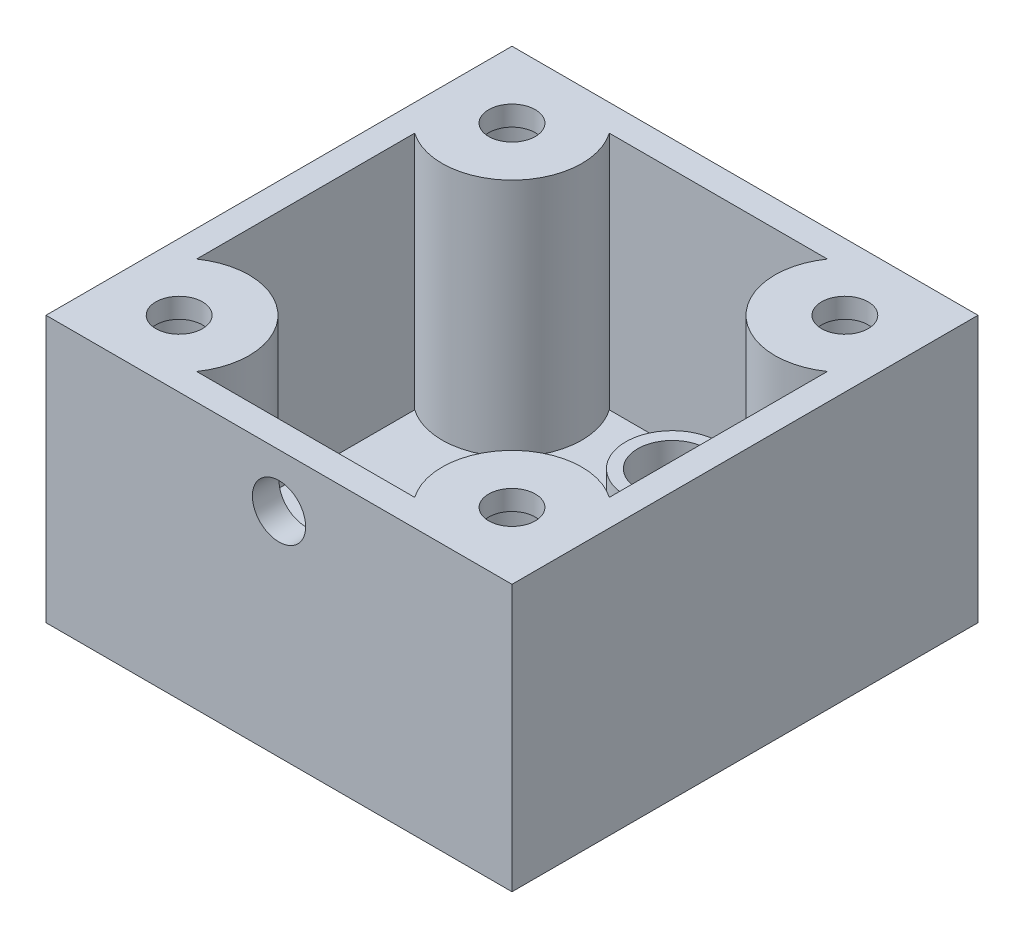
SolidWorks part; units mm, degrees
ref_plane "Front Plane" through (0, 0, 0) normal (0, 0, 1) x (1, 0, 0)
ref_plane "Top Plane" through (0, 0, 0) normal (0, 1, 0) x (1, 0, 0)
ref_plane "Right Plane" through (0, 0, 0) normal (1, 0, 0) x (0, 0, -1)
sketch "Sketch2" plane through (0, 0, 0) normal (0, 1, 0) x (1, 0, 0)
  line L1 (-17.5, -17.5) -> (17.5, -17.5)
  line L2 (-17.5, -17.5) -> (-17.5, 17.5)
  line L3 (-17.5, 17.5) -> (17.5, 17.5)
  line L4 (17.5, -17.5) -> (17.5, 17.5)
  line L5 (-17.5, -17.5) -> (17.5, 17.5) construction
  line L6 (-17.5, 17.5) -> (17.5, -17.5) construction
  point P0 (0, 0)
  dimension "D1" = 35
  dimension "D2" = 35
extrude "Boss-Extrude1" add sketch "Sketch2" against normal blind 20
sketch "Sketch3" plane through (0, 0, 0) normal (0, 1, 0) x (1, 0, 0)
  circle A0 centre (0, -4.7868) radius 6
  circle A1 centre (0, 8.5) radius 2.6
  dimension "D1" = 12
  dimension "D2" = 5.2
sketch "Sketch4" plane through (0, 0, 0) normal (0, 1, 0) x (1, 0, 0)
  line L0 (17.5, 17.5) -> (-17.5, 17.5) construction
  line L1 (-17.5, 17.5) -> (-17.5, -17.5) construction
  line L2 (-17.5, -17.5) -> (17.5, -17.5) construction
  line L3 (17.5, -17.5) -> (17.5, 17.5) construction
  circle A0 centre (-12.5, 12.5) radius 3.25
  circle A1 centre (12.5, 12.5) radius 3.25
  circle A2 centre (-12.5, -12.5) radius 3.25
  circle A3 centre (12.5, -12.5) radius 3.25
  dimension "D1" = 6.5
  dimension "D4" = 6.5
  dimension "D5" = 6.5
  dimension "D7" = 6.5
  dimension "D2" = 5
  dimension "D3" = 5
  dimension "D6" = 5
  dimension "D8" = 5
extrude "Cut-Extrude1" cut sketch "Sketch4" against normal through all from offset 1.5 offset against normal yes
extrude "holes" [suppressed] cut sketch "Sketch3" against normal through all
sketch "Sketch5" plane through (0, 0, 0) normal (0, 1, 0) x (1, 0, 0)
  line L0 (-17.5, 17.5) -> (17.5, -17.5) construction
  line L1 (-17.5, -17.5) -> (17.5, 17.5) construction
  line L2 (-8.1916, 15.5) -> (0, 15.5)
  line L3 (-15.5, 8.1916) -> (-15.5, 0)
  line L6 (17.5, 17.5) -> (-17.5, -17.5) construction
  line L7 (-17.5, 17.5) -> (17.5, -17.5) construction
  line L10 (17.5, -17.5) -> (-17.5, 17.5) construction
  line L11 (17.5, 17.5) -> (-17.5, -17.5) construction
  line L14 (-17.5, -17.5) -> (17.5, 17.5) construction
  line L15 (17.5, -17.5) -> (-17.5, 17.5) construction
  line L16 (-17.5, 17.5) -> (-17.5, -17.5) construction
  line L17 (17.5, 17.5) -> (-17.5, 17.5) construction
  line L18 (8.1916, 15.5) -> (0, 15.5)
  line L19 (15.5, 8.1916) -> (15.5, 0)
  line L20 (15.5, -8.1916) -> (15.5, 0)
  line L21 (8.1916, -15.5) -> (0, -15.5)
  line L22 (-8.1916, -15.5) -> (0, -15.5)
  line L23 (-15.5, -8.1916) -> (-15.5, 0)
  arc A0 (-8.1916, 15.5) -> (-15.5, 8.1916) centre (-12.5, 12.5) cw
  arc A1 (15.5, 8.1916) -> (8.1916, 15.5) centre (12.5, 12.5) cw
  arc A2 (8.1916, -15.5) -> (15.5, -8.1916) centre (12.5, -12.5) cw
  arc A3 (-15.5, -8.1916) -> (-8.1916, -15.5) centre (-12.5, -12.5) cw
  point P11 (-12.5, 12.5)
  point P25 (12.5, 12.5)
  point P35 (12.5, -12.5)
  point P45 (-12.5, -12.5)
  point P48 (0.3754, 0)
  point P57 (0, 0)
  dimension "D3" = 5.25
  dimension "D1" = 2
  dimension "D2" = 2
extrude "cavity" cut sketch "Sketch5" against normal offset from surface (18 mm away) 2 up to face at (-12.5, -20, 15.75)
sketch "Sketch7" plane through (0, -18, 0) normal (0, 1, 0) x (1, 0, 0)
  circle A0 centre (0, 8.5) radius 3.5
  circle A1 centre (0, 8.5) radius 2.575
  dimension "D1" = 7
extrude "LED boss" [suppressed] add sketch "Sketch7" along normal blind 2
sketch "Sketch10" plane through (0, -18, 0) normal (0, 1, 0) x (1, 0, 0)
  circle A0 centre (0, 12.0408) radius 2.6
  circle A1 centre (0, 12.0408) radius 3.5
  dimension "D1" = 5.2
  dimension "D2" = 7
extrude "Boss-Extrude4" add sketch "Sketch10" along normal blind 2
sketch "Sketch9" plane through (0, -18, 0) normal (0, 1, 0) x (1, 0, 0)
  line L0 (6.4, -1.9212) -> (6.4, -7.0788)
  line L1 (-17.5, -17.5) -> (17.5, -17.5) construction
  arc A0 (6.4, -1.9212) -> (6.4, -7.0788) centre (0, -4.5) ccw
  circle A1 centre (0, 12.0408) radius 2.6
  circle A2 centre (0, 12.0408) radius 2.6 construction
  point P11 (-6.9, -4.5)
  dimension "D1" = 13.8
  dimension "D2" = 5.2
  dimension "D3" = 13
  dimension "D4" = 13.3
sketch "Sketch8"
  circle A0 centre (-12.5, 12.5) radius 1.75
  circle A1 centre (12.5, 12.5) radius 1.75
  circle A2 centre (12.5, -12.5) radius 1.75
  circle A3 centre (-12.5, -12.5) radius 1.75
  point P12 (0, 0)
  dimension "D1" = 3.5
  dimension "D2" = 4
extrude "M3 holes" cut sketch "Sketch8" against normal through all
extrude "holess" cut sketch "Sketch9" against normal through all
sketch "Sketch12" plane through (0, 0, 17.5) normal (0, 0, 1) x (1, 0, 0)
  line L0 (-17.5, 0) -> (17.5, 0) construction
  circle A0 centre (0, -4) radius 2
  point P4 (0, 0)
  dimension "D1" = 4
extrude "Cut-Extrude8" cut sketch "Sketch12" against normal up to next
equation "\"M3-CBORE-DIA\"= 6.5"
equation "\"M3-HEX-DIA\"= 5.5"
equation "\"D2@Sketch2\"=\"D1@Sketch2\""
equation "\"D1@Sketch4\"=\"M3-CBORE-DIA\""
equation "\"D3@Sketch4\"=\"D2@Sketch4\""
equation "\"D4@Sketch4\"=\"D1@Sketch4\""
equation "\"D5@Sketch4\"=\"D1@Sketch4\""
equation "\"D6@Sketch4\"=\"D2@Sketch4\""
equation "\"D7@Sketch4\"=\"D1@Sketch4\""
equation "\"D8@Sketch4\"=\"D2@Sketch4\""
equation "\"M3-CLEARANCE\"= 3.5"
equation "\"D1@Sketch8\"=\"M3-CLEARANCE\""
equation "\"D2@Sketch5\"=\"D1@Sketch5\""
equation "\"D3@Sketch5\"=\"M3-CBORE-DIA\"/2 + 2"
equation "\"LED-HOLE-DIA\"= 5.2"
equation "\"D1@Sketch10\"=\"LED-HOLE-DIA\""
equation "\"D2@Sketch9\"=\"LED-HOLE-DIA\""
